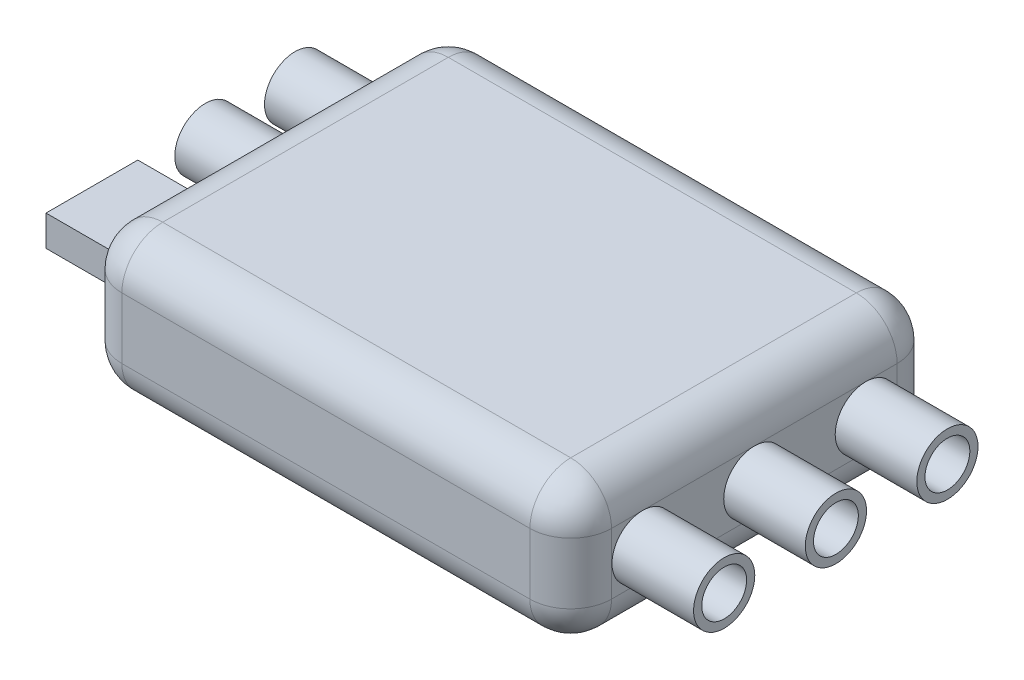
SolidWorks part; units mm, degrees
ref_plane "Front Plane" through (0, 0, 0) normal (0, 0, 1) x (1, 0, 0)
ref_plane "Top Plane" through (0, 0, 0) normal (0, 1, 0) x (1, 0, 0)
ref_plane "Right Plane" through (0, 0, 0) normal (1, 0, 0) x (0, 0, -1)
sketch "Sketch1" plane through (0, 0, 0) normal (0, 1, 0) x (1, 0, 0)
  line L1 (10, -9) -> (-10, -9)
  line L2 (12, -7) -> (12, 7)
  line L3 (10, 9) -> (-10, 9)
  line L4 (-12, -7) -> (-12, 7)
  line L5 (12, -9) -> (-12, 9) construction
  line L6 (12, 9) -> (-12, -9) construction
  arc A0 (-10, -9) -> (-12, -7) centre (-10, -7) cw
  arc A1 (12, 7) -> (10, 9) centre (10, 7) ccw
  arc A2 (-10, 9) -> (-12, 7) centre (-10, 7) ccw
  arc A3 (10, -9) -> (12, -7) centre (10, -7) ccw
  point P0 (0, 0)
  dimension "D3" = 2
  dimension "D1" = 24
  dimension "D2" = 18
extrude "Boss-Extrude1" add sketch "Sketch1" along normal blind 7
fillet "Fillet1" radius 2 16 edges at (0, 0, 9) (11.4142, 0, 8.4142) (12, 0, 0) (11.4142, 0, -8.4142) (0, 0, -9) (-11.4142, 0, -8.4142) (-12, 0, 0) (-11.4142, 0, 8.4142) (-12, 7, 0) (-11.4142, 7, -8.4142) (0, 7, -9) (11.4142, 7, -8.4142) (12, 7, 0) (11.4142, 7, 8.4142) (0, 7, 9) (-11.4142, 7, 8.4142)
sketch "Sketch2" plane through (12, 0, 0) normal (1, 0, 0) x (0, 0, -1)
  line L0 (-7, 3.5) -> (7, 3.5) construction
  line L1 (-7, 5) -> (-7, 2) construction
  line L2 (7, 5) -> (7, 2) construction
  circle A0 centre (0, 3.5) radius 1.1
  circle A1 centre (0, 3.5) radius 1.5
  circle A2 centre (-5.4766, 3.5) radius 1.1
  circle A3 centre (-5.4766, 3.5) radius 1.5
  circle A4 centre (5.4648, 3.5) radius 1.1
  circle A5 centre (5.4648, 3.5) radius 1.5
  point P15 (-5.4766, 3.5)
  point P16 (0, 0)
  dimension "D1" = 3
  dimension "D2" = 0.4
extrude "Boss-Extrude2" add sketch "Sketch2" along normal blind 4
sketch "Sketch3" plane through (-12, 0, 0) normal (-1, 0, 0) x (0, 0, 1)
  line L0 (-7, 3.5) -> (7, 3.5) construction
  line L1 (-7, 5) -> (-7, 2) construction
  line L2 (7, 5) -> (7, 2) construction
  line L4 (6.7203, 2.75) -> (2.2203, 2.75)
  line L5 (6.7203, 2.75) -> (6.7203, 4.25)
  line L6 (6.7203, 4.25) -> (2.2203, 4.25)
  line L7 (2.2203, 2.75) -> (2.2203, 4.25)
  circle A0 centre (-1.0911, 3.5) radius 1.1
  circle A1 centre (-1.0911, 3.5) radius 1.5
  circle A2 centre (-5.4911, 3.5) radius 1.1
  circle A3 centre (-5.4911, 3.5) radius 1.5
  dimension "D3" = 3
  dimension "D4" = 0.4
  dimension "D5" = 4.4
  dimension "D1" = 4.5
  dimension "D2" = 1.5
extrude "Boss-Extrude3" add sketch "Sketch3" along normal blind 4
